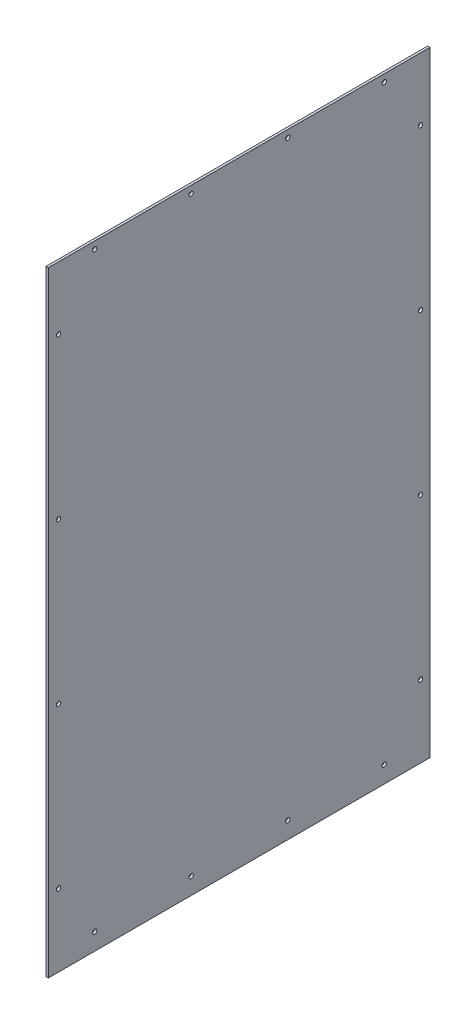
SolidWorks part; units mm, degrees
material "Acrylic (Medium-high impact)"
ref_plane "Front Plane" through (0, 0, 0) normal (0, 0, 1) x (1, 0, 0)
ref_plane "Top Plane" through (0, 0, 0) normal (0, 1, 0) x (1, 0, 0)
ref_plane "Right Plane" through (0, 0, 0) normal (1, 0, 0) x (0, 0, -1)
sketch "Sketch1" plane through (0, 0, 0) normal (1, 0, 0) x (0, 0, -1)
  line L0 (-251.1933, 404.8633) -> (-251.1933, 407.9367) construction
  line L1 (251.1933, -404.8633) -> (-251.1933, -404.8633)
  line L2 (251.1933, -404.8633) -> (251.1933, 404.8633)
  line L3 (251.1933, 404.8633) -> (-251.1933, 404.8633)
  line L4 (-251.1933, -404.8633) -> (-251.1933, 404.8633)
  line L5 (251.1933, -404.8633) -> (-251.1933, 404.8633) construction
  line L6 (251.1933, 404.8633) -> (-251.1933, -404.8633) construction
  point P0 (0, 0)
  dimension "D1" = 502.3866
  dimension "D2" = 3.0734
  dimension "D3" = 812.8
extrude "SidePanel" add sketch "Sketch1" along normal blind 3.0734
sketch "Sketch2" plane through (3.0734, 0, 0) normal (1, 0, 0) x (0, 0, -1)
  line L0 (190.9699, 404.8633) -> (190.9699, 385.8133) construction
  line L1 (251.1933, 404.8633) -> (-251.1933, 404.8633) construction
  line L3 (190.9699, -392.1633) -> (190.9699, -373.1133) construction
  line L4 (190.9699, 395.3383) -> (229.0699, 395.3383) construction
  line L5 (-251.1933, -404.8633) -> (251.1933, -404.8633) construction
  line L7 (229.0699, 395.3383) -> (248.1199, 395.3383) construction
  line L8 (248.1199, 395.3383) -> (251.1933, 395.3383) construction
  line L9 (251.1933, -404.8633) -> (251.1933, 404.8633) construction
  circle A0 centre (190.9699, 395.3383) radius 2.8956
  circle A1 centre (190.9699, -382.6383) radius 2.8956
  dimension "D3" = 5.7912
  dimension "D1" = 19.05
  dimension "D4" = 19.05
  dimension "D5" = 12.7
  dimension "D2" = 38.1
  dimension "D6" = 19.05
  dimension "D7" = 3.0734
extrude "TopBottomHoleMaster" cut sketch "Sketch2" against normal through all
pattern_linear "LPattern1" count 4 spacing 127.0677 along (0, 0, 1) of "TopBottomHoleMaster"
sketch "Sketch3" plane through (3.0734, 0, 0) normal (1, 0, 0) x (0, 0, -1)
  line L0 (251.1933, 322.2117) -> (248.1199, 322.2117) construction
  line L1 (251.1933, -404.8633) -> (251.1933, 404.8633) construction
  line L2 (248.1199, 322.2117) -> (229.0699, 322.2117) construction
  line L3 (251.1933, 404.8633) -> (251.1933, 407.9367) construction
  line L4 (251.1933, 404.8633) -> (-251.1933, 404.8633) construction
  line L5 (-250.5583, 322.2117) -> (-247.3833, 322.2117) construction
  line L6 (-250.5583, 322.2117) -> (-253.7333, 322.2117) construction
  line L8 (-247.3833, 322.2117) -> (-228.3333, 322.2117) construction
  line L11 (-253.7333, 322.2117) -> (-256.8067, 322.2117) construction
  line L12 (251.1933, -404.8633) -> (251.1933, 404.8633) construction
  circle A0 centre (-237.8583, 322.2117) radius 2.8956
  circle A1 centre (238.5949, 322.2117) radius 2.8956
  dimension "D1" = 3.0734
  dimension "D5" = 5.7912
  dimension "D2" = 19.05
  dimension "D3" = 3.0734
  dimension "D4" = 85.725
  dimension "D6" = 3.175
  dimension "D8" = 3.0734
  dimension "D9" = 508
extrude "RearHolesMaster" cut sketch "Sketch3" against normal through all
pattern_linear "LPattern2" count 4 spacing 210.5745 along (0, -1, 0) of "RearHolesMaster"
sketch "Sketch4" plane through (0, 0, 0) normal (-1, 0, 0) x (0, 0, 1)
  line L0 (-238.7655, -312.4023) -> (-238.7655, -404.8633) construction
  line L1 (251.1933, -404.8633) -> (-251.1933, -404.8633) construction
  line L2 (-190.9699, -385.5339) -> (-238.7655, -385.5339) construction
  line L3 (-238.2575, -385.5339) -> (-239.2735, -385.5339)
  line L4 (-239.2735, -385.5339) -> (-239.2735, -384.2639)
  line L5 (-239.2735, -384.2639) -> (-239.7815, -384.2639)
  line L6 (-239.7815, -384.2639) -> (-238.7655, -382.9939)
  line L7 (-238.2575, -385.5339) -> (-238.2575, -384.2639)
  line L8 (-238.2575, -384.2639) -> (-237.7495, -384.2639)
  line L9 (-237.7495, -384.2639) -> (-238.7655, -382.9939)
  circle A1 centre (-190.9699, -382.6383) radius 2.8956 construction
  circle A2 centre (-238.5949, -309.5117) radius 2.8956 construction
  dimension "D1" = 1.016
  dimension "D2" = 2.032
  dimension "D3" = 1.27
  dimension "D4" = 1.27
extrude "Cut-Extrude1" cut sketch "Sketch4" against normal blind 2.54
equation "\"Height\"= 32in"
equation "\"Width\"= 23in"
equation "\"Depth\"= 20in"
equation "\"Plexi\"= .121in"
equation "\"Cutwidth\"= .016in"
equation "\"Earsize\"= 1in + \"Cutwidth\" /2"
equation "\"Slotsize\" = 1in - \"CutWidth\" / 2"
equation "\"InnerWidth\" = \"Width\" - 2* \"Plexi\""
equation "\"InnerHeight\" = \"Height\" -2 * \"Plexi\""
equation "\"InnerDepth\" = \"Depth\" - 2*\"Plexi\""
equation "\"RearHoleSpacing\" = (\"Width\" - 2*\"RearHolesBorder\") / (\"RearNumHoles\"-1)"
equation "\"RivetDia\" = .228in"
equation "\"SlotDepth\" = \"Plexi\" + 0.75in + .005in"
equation "\"SideSlotWidth\"   = \"Plexi\"+.005in"
equation "\"SidePanelVertSpacing\" = (\"Height\"-2*(1.75-\"Plexi\")) / 5"
equation "\"BottomPanelSideHoleSpacing\" = (\"InnerDepth\"-2*(1.75-\"Plexi\")) / 4"
equation "\"D1@Sketch1\"=\"TopDepth\""
equation "\"D2@Sketch1\"=\"Plexi\""
equation "\"D1@SidePanel\"=\"Plexi\""
equation "\"MagnetThickness\"= 0.125in"
equation "\"MagnetDiameter\"= 12mm"
equation "\"DoorPlexi\" = \"Plexi\""
equation "\"Boxsize\" = .75in"
equation "\"Boxinner\" = .625in"
equation "\"CornerCube\" = 0.75in"
equation "\"FingerLength\" = 1.125in"
equation "\"RearNumHoles\" = 4"
equation "\"RearHolesBorder\" = 2.25"
equation "\"RearBarLength\" = (\"InnerWidth\"-2*\"CornerCube\")"
equation "\"RearTopNumHoles\" = 4"
equation "\"RearTopHolesBorder\" = 3.1"
equation "\"RearTopHolesSpacing\" = (\"Width\" - 2*\"RearTopHolesBorder\") / (\"RearTopNumHoles\"-1)"
equation "\"SideTopNumHoles\" = 4"
equation "\"SideTopHoleOffset\"=\"CornerCube\"+\"FingerLength\"+\"Plexi\"+.5"
equation "\"SideTopHoleSpacing\" = (\"TopBarDepth\"-2*\"SideTopHoleOffset\") / (\"SideTopNumHoles\"-1)"
equation "\"SideHorizNumHoles\" = 4"
equation "\"SideHorizHoleBorder\" = 1.50"
equation "\"SideHorizHoleSpacing\" = (\"TopBarDepth\"-2*\"SideHorizHoleBorder\") / (\"SideHorizNumHoles\"-1)"
equation "\"SideVertNumHoles\" = 4"
equation "\"SideVertHolesBorder\" = \"CornerCube\"+\"FingerLength\"+1.50"
equation "\"SideVertHoleSpacing\" = (\"SideVertBarLength\" - 2*(\"SideVertHolesBorder\"-\"Plexi\"-\"CornerCube\")) / (\"SideVertNumHoles\"-1)"
equation "\"FrontDoorGap\" = .1in"
equation "\"TopDepth\" = \"Depth\"-\"DoorPlexi\"-\"FrontDoorGap\""
equation "\"TopBarDepth\" = \"Depth\"-\"DoorPlexi\"-\"Plexi\"-2*\"MagnetThickness\"-2*\"CornerCube\""
equation "\"D1@Sketch2\"=\"Boxsize\""
equation "\"D3@Sketch2\"=\"RivetDia\""
equation "\"D4@Sketch2\"=\"Boxsize\""
equation "\"D3@LPattern1\"=\"SideHorizHoleSpacing\""
equation "\"D1@LPattern1\"=\"SideHorizNumHoles\""
equation "\"D1@Sketch3\"=\"Plexi\""
equation "\"D2@Sketch3\"=\"Boxsize\""
equation "\"D3@Sketch3\"=\"Plexi\""
equation "\"D4@Sketch3\"=\"SideVertHolesBorder\""
equation "\"D5@Sketch3\"=\"RivetDia\""
equation "\"D3@LPattern2\"=\"SideVertHoleSpacing\""
equation "\"D1@LPattern2\"=\"SideVertNumHoles\""
equation "\"BasePlateThickness\" = 0.5in"
equation "\"SideVertBarLength\"=\"Height\"-\"BasePlateThickness\"-2*\"CornerCube\"-\"Plexi\""
equation "\"RearSideVertNumHoles\" = 4"
equation "\"RearSideVertHolesBorder\" = 2.4"
equation "\"RearSideVertHoleSpacing\" = (\"SideVertBarLength\" - 2*(\"RearSideVertHolesBorder\"-\"Plexi\"-\"CornerCube\")) / (\"RearSideVertNumHoles\"-1)"
equation "\"D5@Sketch2\"=\"BasePlateThickness\""
equation "\"D3@Sketch1\"=\"Height\""
equation "\"D6@Sketch3\"=\"MagnetThickness\""
equation "\"D8@Sketch3\"=\"DoorPlexi\""
equation "\"D9@Sketch3\"=\"Depth\""
equation "\"D7@Sketch2\"=\"Plexi\""
equation "\"D6@Sketch2\"=\"Boxsize\""
equation "\"D2@Sketch2\"=\"SideHorizHoleBorder\""
equation "\"EBWidth\" = 9in"
equation "\"ComponentMountDia\"=0.1770"
equation "\"ShelfThickness\" = .1250in"
equation "\"BasePlateWidth\" = \"Width\"+\"EBWidth\"-2*\"Plexi\""
equation "\"BasePlateDepth\" = \"TopBarDepth\"+2*\"CornerCube\""
equation "\"BoxsizeHalf\" = \"Boxsize\"/2"
equation "\"FingerWidth\" = .625in"
equation "\"Rivet3_16Dia\" = .191in"
equation "\"BinderPostDia\" = .228in"
equation "\"CoolerDepth\" = 12in"
equation "\"ShelfGap\" = 0.5in"
equation "\"ShelfDepth\" = \"TopBarDepth\"+\"CornerCube\"-\"CoolerDepth\""
equation "\"ShelfBarDepth\"=\"ShelfDepth\"-2*\"CornerCube\""
equation "\"ShelfWidth\" = \"EBWidth\"-\"ShelfGap\""
equation "\"ShelfBarWidth\" = \"EBWidth\"-\"Boxsize\""
equation "\"ShelfBarWidthShort\" = \"ShelfBarWidth\"-\"Boxsize\"-\"ShelfGap\""
equation "\"ShelfHeight1\" = 13in"
equation "\"ShelfHeight2\" = 24in"
equation "\"IntakeWidth\"=4in"
equation "\"IntakeHeight\"=2in"
equation "\"ExhaustWidth\"=4in"
equation "\"ExhaustHeight\"=2in"
equation "\"VentSpacing\"=7in"
equation "\"VentVertLocation\"=12.75in"
equation "\"AngleBracketLengthShort\"=.625in"
equation "\"AngleBracketLengthLong\"=1in"
equation "\"AngleBracketWidth\"=.5in"
equation "\"AngleBracketThickness\"=.125in"
equation "\"AngleBracketHolePosShort\"=.358in"
equation "\"AngleBracketHolePosLong\"=.7in"
equation "\"AngleBracketHoleDia\"=\"Rivet3_16Dia\""
equation "\"ShelfBarAngleHole\"=\"ShelfGap\"+\"Boxsize\"+\"AngleBracketHolePosShort\""
equation "\"PSBracketThickness\" = .0641in"
equation "\"EBForwardMountOffset\" = 4.0in"
equation "\"EBForwardMount\" = 2*\"Boxsize\"+\"CoolerDepth\"+\"EBForwardMountOffset\""
equation "\"EBRearwardMountOffset\" = 1.5in"
equation "\"EBRearwardMount\"= \"Boxsize\"+\"EBRearwardMountOffset\""
equation "\"MagSealWidth\" = \"InnerWidth\""
equation "\"MagSealHeight\" = \"Height\"-\"BasePlateThickness\"-\"Plexi\""
equation "\"MagWidth\" = .500in"
equation "\"SiliconeSealOD\" = .3125in"
equation "\"SiliconeSealID\" = .1875in"
equation "\"SiliconeSealWidth\" = \"MagSealWidth\" - 2*\"MagWidth\"-\"SiliconeSealOD\""
equation "\"SiliconeSealHeigth\" = \"MagSealHeight\" - 2*\"MagWidth\"-\"SiliconeSealOD\""
equation "\"HooknLoopThick\" = .085in"
equation "\"HooknLoopWidth\" = 0.75in"
equation "\"HooknLoopHeigth\" = 0.75in"
equation "\"RivNutHeight\" = 0.015in"
